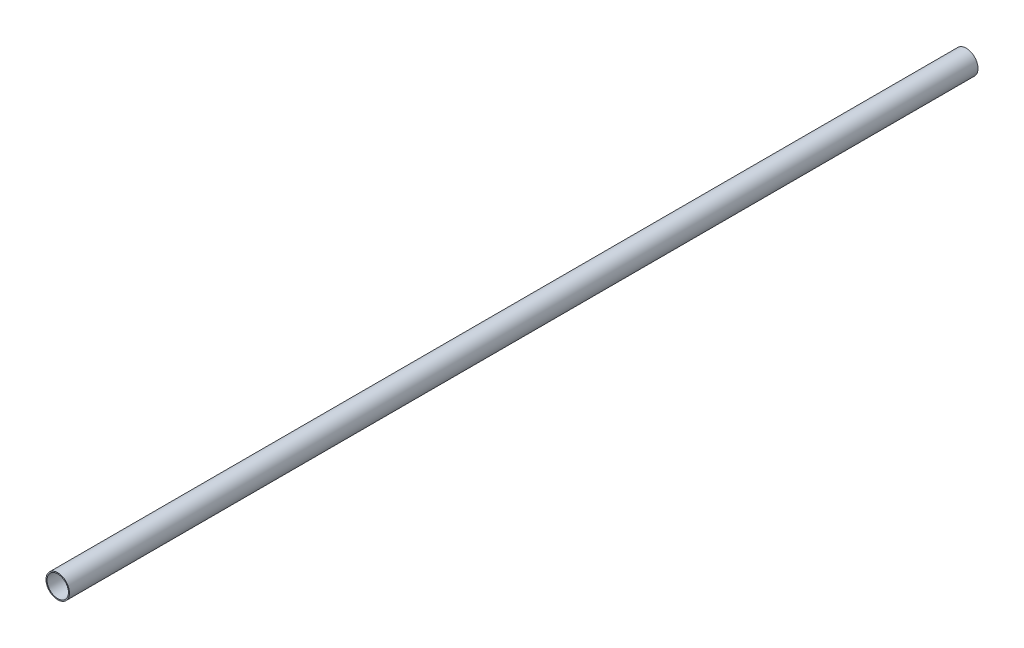
SolidWorks part; units mm, degrees
material "Carbon Fiber Tube - UD Approx"
ref_plane "Front Plane" through (0, 0, 0) normal (0, 0, 1) x (1, 0, 0)
ref_plane "Top Plane" through (0, 0, 0) normal (0, 1, 0) x (1, 0, 0)
ref_plane "Right Plane" through (0, 0, 0) normal (1, 0, 0) x (0, 0, -1)
sketch "Sketch1" plane through (0, 0, 0) normal (0, 0, 1) x (1, 0, 0)
  circle A0 centre (0, 0) radius 11
  circle A1 centre (0, 0) radius 10
  dimension "D1" = 22
  dimension "D2" = 20
extrude "Boss-Extrude1" add sketch "Sketch1" along normal blind 850
